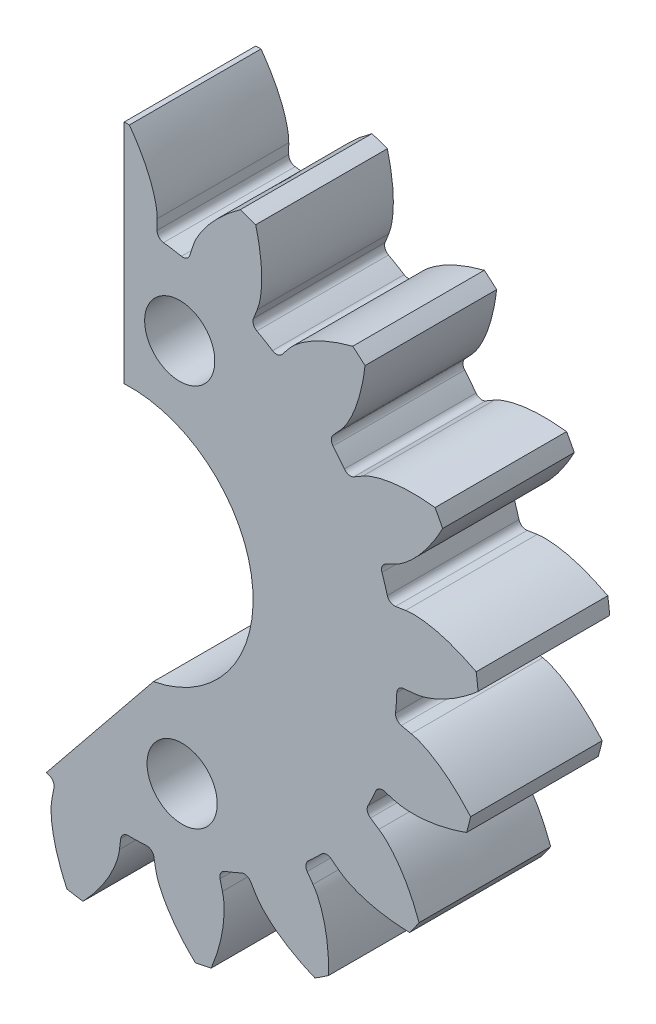
SolidWorks part; units mm, degrees
ref_plane "Front" through (0, 0, 0) normal (0, 0, 1) x (1, 0, 0)
ref_plane "Top" through (0, 0, 0) normal (0, 1, 0) x (1, 0, 0)
ref_plane "Right" through (0, 0, 0) normal (1, 0, 0) x (0, 0, -1)
sketch "Sketch1" plane through (0, 0, 0) normal (0, 0, 1) x (1, 0, 0)
  line L68 (2.1427, 9.4464) -> (2.0368, 9.1165)
  line L69 (0.916, 9.2963) -> (0.9185, 9.6427)
  line L70 (-1.4144, 9.5825) -> (-1.394, 9.2367)
  line L71 (-2.504, 8.9994) -> (-2.6268, 9.3234)
  line L72 (-4.7805, 8.4245) -> (-4.6366, 8.1093)
  line L73 (-5.5859, 7.4871) -> (-5.8174, 7.7449)
  line L74 (-7.501, 6.1287) -> (-7.2529, 5.8868)
  line L75 (-7.9134, 4.9637) -> (-8.2224, 5.1204)
  line L76 (-9.2084, 3.0052) -> (-8.8897, 2.8692)
  line L77 (-9.1721, 1.7699) -> (-9.5168, 1.8043)
  line L78 (-9.6722, -0.5242) -> (-9.3259, -0.5358)
  line L79 (-9.1921, -1.663) -> (-9.526, -1.7554)
  line L80 (-8.8296, -3.9828) -> (-8.5026, -3.8686)
  line L81 (-7.9706, -4.8713) -> (-8.2486, -5.078)
  line L82 (-6.7946, -6.9035) -> (-6.5309, -6.6788)
  line L83 (-5.6727, -7.4216) -> (-5.8572, -7.7148)
  line L84 (-3.842, -8.8918) -> (-3.6772, -8.587)
  line L85 (-2.6086, -8.9696) -> (-2.6747, -9.3097)
  line L86 (-0.3704, -9.6793) -> (-0.3269, -9.3356)
  line L87 (0.8078, -9.3063) -> (0.8689, -9.6473)
  line L88 (3.1511, -9.1595) -> (3.0675, -8.8232)
  line L89 (4.115, -8.3861) -> (4.2953, -8.6819)
  line L90 (6.2471, -7.4026) -> (6.0477, -7.1193)
  line L91 (6.8665, -6.3332) -> (7.1415, -6.544)
  line L92 (8.4994, -4.646) -> (8.2111, -4.4539)
  line L93 (8.6907, -3.4251) -> (9.0232, -3.5223)
  line L94 (9.6038, -1.2619) -> (9.2656, -1.1869)
  line L95 (9.3411, -0.0544) -> (9.6863, -0.0249)
  line L96 (9.4111, 2.2926) -> (9.0686, 2.2404)
  line L97 (8.73, 3.3237) -> (9.0412, 3.4759)
  line L98 (7.9475, 5.5374) -> (7.6469, 5.365)
  line L99 (6.9398, 6.2529) -> (7.1751, 6.5072)
  line L100 (5.4104, 8.0345) -> (5.1925, 7.7651)
  line L101 (4.2123, 8.3376) -> (4.3399, 8.6597)
  circle A0 centre (0, 0) radius 1.5
  arc A136 (4.2867, 11.1494) -> (3.764, 11.3366) centre (0, 0) ccw
  arc A137 (1.7491, 8.9466) -> (2.0368, 9.1165) centre (1.7973, 9.1934) ccw
  arc A138 (1.7491, 8.9466) -> (1.1361, 9.0449) centre (0, 0) ccw
  arc A139 (0.916, 9.2963) -> (1.1361, 9.0449) centre (1.1675, 9.2944) ccw
  arc A140 (-0.0304, 11.945) -> (-0.5854, 11.9307) centre (0, 0) ccw
  arc A141 (-1.6009, 8.9743) -> (-1.394, 9.2367) centre (-1.6451, 9.2219) ccw
  arc A142 (-1.6009, 8.9743) -> (-2.208, 8.8445) centre (0, 0) ccw
  arc A143 (-2.504, 8.9994) -> (-2.208, 8.8445) centre (-2.2689, 9.0885) ccw
  arc A144 (-4.3434, 11.1274) -> (-4.8558, 10.9136) centre (0, 0) ccw
  arc A145 (-4.7347, 7.79) -> (-4.6366, 8.1093) centre (-4.8653, 8.0049) ccw
  arc A146 (-4.7347, 7.79) -> (-5.2539, 7.4497) centre (0, 0) ccw
  arc A147 (-5.5859, 7.4871) -> (-5.2539, 7.4497) centre (-5.3988, 7.6552) ccw
  arc A148 (-8.0698, 8.807) -> (-8.4703, 8.4225) centre (0, 0) ccw
  arc A149 (-7.229, 5.5536) -> (-7.2529, 5.8868) centre (-7.4285, 5.7068) ccw
  arc A150 (-7.229, 5.5536) -> (-7.5902, 5.0487) centre (0, 0) ccw
  arc A151 (-7.9134, 4.9637) -> (-7.5902, 5.0487) centre (-7.7996, 5.188) ccw
  arc A152 (-10.7063, 5.2971) -> (-10.9409, 4.7939) centre (0, 0) ccw
  arc A153 (-8.7471, 2.5671) -> (-8.8897, 2.8692) centre (-8.9884, 2.6379) ccw
  arc A154 (-8.7471, 2.5671) -> (-8.9015, 1.9659) centre (0, 0) ccw
  arc A155 (-9.1721, 1.7699) -> (-8.9015, 1.9659) centre (-9.147, 2.0201) ccw
  arc A156 (-11.8969, 1.0719) -> (-11.9338, 0.5179) centre (0, 0) ccw
  arc A157 (-9.0837, -0.766) -> (-9.3259, -0.5358) centre (-9.3343, -0.7872) ccw
  arc A158 (-9.0837, -0.766) -> (-9.0105, -1.3825) centre (0, 0) ccw
  arc A159 (-9.1921, -1.663) -> (-9.0105, -1.3825) centre (-9.2591, -1.4206) ccw
  arc A160 (-11.4807, -3.2982) -> (-11.3151, -3.8281) centre (0, 0) ccw
  arc A161 (-8.1936, -3.9957) -> (-8.5026, -3.8686) centre (-8.4196, -4.106) ccw
  arc A162 (-8.1936, -3.9957) -> (-7.9027, -4.5441) centre (0, 0) ccw
  arc A163 (-7.9706, -4.8713) -> (-7.9027, -4.5441) centre (-8.1207, -4.6695) ccw
  arc A164 (-9.514, -7.2228) -> (-9.1681, -7.6571) centre (0, 0) ccw
  arc A165 (-6.1969, -6.6858) -> (-6.5309, -6.6788) centre (-6.3678, -6.8702) ccw
  arc A166 (-6.1969, -6.6858) -> (-5.7275, -7.092) centre (0, 0) ccw
  arc A167 (-5.6727, -7.4216) -> (-5.7275, -7.092) centre (-5.8855, -7.2877) ccw
  arc A168 (-6.2624, -10.1719) -> (-5.783, -10.4519) centre (0, 0) ccw
  arc A169 (-3.3632, -8.4729) -> (-3.6772, -8.587) centre (-3.456, -8.7066) ccw
  arc A170 (-3.3632, -8.4729) -> (-2.7788, -8.6821) centre (0, 0) ccw
  arc A171 (-2.6086, -8.9696) -> (-2.7788, -8.6821) centre (-2.8554, -8.9216) ccw
  arc A172 (-2.165, -11.7472) -> (-1.6168, -11.8352) centre (0, 0) ccw
  arc A173 (-0.0754, -9.1157) -> (-0.3269, -9.3356) centre (-0.0774, -9.3671) ccw
  arc A174 (-0.0754, -9.1157) -> (0.5452, -9.0997) centre (0, 0) ccw
  arc A175 (0.8078, -9.3063) -> (0.5452, -9.0997) centre (0.5602, -9.3507) ccw
  arc A176 (2.2248, -11.7361) -> (2.7677, -11.62) centre (0, 0) ccw
  arc A177 (3.2227, -8.5273) -> (3.0675, -8.8232) centre (3.3116, -8.7626) ccw
  arc A178 (3.2227, -8.5273) -> (3.7956, -8.2882) centre (0, 0) ccw
  arc A179 (4.115, -8.3861) -> (3.7956, -8.2882) centre (3.9003, -8.5169) ccw
  arc A180 (6.3141, -10.1399) -> (6.7785, -9.8355) centre (0, 0) ccw
  arc A181 (6.0855, -6.7873) -> (6.0477, -7.1193) centre (6.2534, -6.9746) ccw
  arc A182 (6.0855, -6.7873) -> (6.5333, -6.3574) centre (0, 0) ccw
  arc A183 (6.8665, -6.3332) -> (6.5333, -6.3574) centre (6.7135, -6.5328) ccw
  arc A184 (9.5507, -7.1742) -> (9.8737, -6.7227) centre (0, 0) ccw
  arc A185 (8.1264, -4.1307) -> (8.2111, -4.4539) centre (8.3506, -4.2446) ccw
  arc A186 (8.1264, -4.1307) -> (8.3887, -3.568) centre (0, 0) ccw
  arc A187 (8.6907, -3.4251) -> (8.3887, -3.568) centre (8.6201, -3.6665) ccw
  arc A188 (11.4974, -3.2397) -> (11.6355, -2.7019) centre (0, 0) ccw
  arc A189 (9.0698, -0.9161) -> (9.2656, -1.1869) centre (9.32, -0.9414) ccw
  arc A190 (9.0698, -0.9161) -> (9.1112, -0.2967) centre (0, 0) ccw
  arc A191 (9.3411, -0.0544) -> (9.1112, -0.2967) centre (9.3625, -0.3049) ccw
  arc A192 (11.8913, 1.1324) -> (11.8258, 1.6838) centre (0, 0) ccw
  arc A193 (8.7883, 2.4221) -> (9.0686, 2.2404) centre (9.0307, 2.489) ccw
  arc A194 (8.7883, 2.4221) -> (8.6031, 3.0146) centre (0, 0) ccw
  arc A195 (8.73, 3.3237) -> (8.6031, 3.0146) centre (8.8404, 3.0978) ccw
  arc A196 (10.6792, 5.3516) -> (10.419, 5.842) centre (0, 0) ccw
  arc A197 (7.3199, 5.4333) -> (7.6469, 5.365) centre (7.5218, 5.5832) ccw
  arc A198 (7.3199, 5.4333) -> (6.9331, 5.9189) centre (0, 0) ccw
  arc A199 (6.9398, 6.2529) -> (6.9331, 5.9189) centre (7.1244, 6.0821) ccw
  arc A200 (8.0248, 8.848) -> (7.605, 9.2113) centre (0, 0) ccw
  arc A201 (4.8629, 7.7106) -> (5.1925, 7.7651) centre (4.997, 7.9233) ccw
  arc A202 (4.8629, 7.7106) -> (4.3268, 8.0237) centre (0, 0) ccw
  arc A203 (4.2123, 8.3376) -> (4.3268, 8.0237) centre (4.4462, 8.245) ccw
  spline S68 degree 3 poles (3.764, 11.3366) (3.2587, 10.9714) (2.6231, 10.3935) (2.2067, 9.6531) (2.1427, 9.4464) knots -0.008485 -0.008485 -0.008485 -0.008485 0.741457 1 1 1 1
  spline S69 degree 3 poles (0.9185, 9.6427) (0.9201, 9.8535) (0.7567, 10.6863) (0.3366, 11.435) (-0.0304, 11.945) knots 0 0 0 0 0.250058 1 1 1 1
  spline S70 degree 3 poles (-0.5854, 11.9307) (-0.9247, 11.4077) (-1.3085, 10.6392) (-1.4294, 9.7984) (-1.4144, 9.5825) knots -0.008485 -0.008485 -0.008485 -0.008485 0.741457 1 1 1 1
  spline S71 degree 3 poles (-2.6268, 9.3234) (-2.7015, 9.5204) (-3.1547, 10.238) (-3.8169, 10.7844) (-4.3434, 11.1274) knots 0 0 0 0 0.250058 1 1 1 1
  spline S72 degree 3 poles (-4.8558, 10.9136) (-4.9832, 10.3033) (-5.0635, 9.4481) (-4.8725, 8.6204) (-4.7805, 8.4245) knots -0.008485 -0.008485 -0.008485 -0.008485 0.741457 1 1 1 1
  spline S73 degree 3 poles (-5.8174, 7.7449) (-5.9583, 7.9016) (-6.64, 8.4071) (-7.455, 8.6773) (-8.0698, 8.807) knots 0 0 0 0 0.250058 1 1 1 1
  spline S74 degree 3 poles (-8.4703, 8.4225) (-8.3687, 7.8074) (-8.1346, 6.9809) (-7.6575, 6.2781) (-7.501, 6.1287) knots -0.008485 -0.008485 -0.008485 -0.008485 0.741457 1 1 1 1
  spline S75 degree 3 poles (-8.2224, 5.1204) (-8.4103, 5.2157) (-9.2286, 5.4407) (-10.0862, 5.3983) (-10.7063, 5.2971) knots 0 0 0 0 0.250058 1 1 1 1
  spline S76 degree 3 poles (-10.9409, 4.7939) (-10.624, 4.2571) (-10.1071, 3.5709) (-9.4083, 3.088) (-9.2084, 3.0052) knots -0.008485 -0.008485 -0.008485 -0.008485 0.741457 1 1 1 1
  spline S77 degree 3 poles (-9.5168, 1.8043) (-9.7265, 1.8253) (-10.5708, 1.7395) (-11.3552, 1.3902) (-11.8969, 1.0719) knots 0 0 0 0 0.250058 1 1 1 1
  spline S78 degree 3 poles (-11.9338, 0.5179) (-11.4444, 0.1318) (-10.7145, -0.3213) (-9.8885, -0.5192) (-9.6722, -0.5242) knots -0.008485 -0.008485 -0.008485 -0.008485 0.741457 1 1 1 1
  spline S79 degree 3 poles (-9.526, -1.7554) (-9.7291, -1.8116) (-10.4854, -2.1966) (-11.0906, -2.8056) (-11.4807, -3.2982) knots 0 0 0 0 0.250058 1 1 1 1
  spline S80 degree 3 poles (-11.3151, -3.8281) (-10.7192, -4.0113) (-9.875, -4.1701) (-9.0332, -4.0563) (-8.8296, -3.9828) knots -0.008485 -0.008485 -0.008485 -0.008485 0.741457 1 1 1 1
  spline S81 degree 3 poles (-8.2486, -5.078) (-8.4177, -5.2038) (-8.9839, -5.836) (-9.3281, -6.6225) (-9.514, -7.2228) knots 0 0 0 0 0.250058 1 1 1 1
  spline S82 degree 3 poles (-9.1681, -7.6571) (-8.5463, -7.6126) (-7.7017, -7.4558) (-6.9579, -7.0456) (-6.7946, -6.9035) knots -0.008485 -0.008485 -0.008485 -0.008485 0.741457 1 1 1 1
  spline S83 degree 3 poles (-5.8572, -7.7148) (-5.9694, -7.8932) (-6.269, -8.6873) (-6.3059, -9.545) (-6.2624, -10.1719) knots 0 0 0 0 0.250058 1 1 1 1
  spline S84 degree 3 poles (-5.783, -10.4519) (-5.2192, -10.1859) (-4.4883, -9.7345) (-3.9429, -9.0833) (-3.842, -8.8918) knots -0.008485 -0.008485 -0.008485 -0.008485 0.741457 1 1 1 1
  spline S85 degree 3 poles (-2.6747, -9.3097) (-2.715, -9.5166) (-2.7074, -10.3653) (-2.432, -11.1784) (-2.165, -11.7472) knots 0 0 0 0 0.250058 1 1 1 1
  spline S86 degree 3 poles (-1.6168, -11.8352) (-1.1872, -11.3834) (-0.6687, -10.6985) (-0.3954, -9.8942) (-0.3704, -9.6793) knots -0.008485 -0.008485 -0.008485 -0.008485 0.741457 1 1 1 1
  spline S87 degree 3 poles (0.8689, -9.6473) (0.9062, -9.8547) (1.2197, -10.6434) (1.7703, -11.3021) (2.2248, -11.7361) knots 0 0 0 0 0.250058 1 1 1 1
  spline S88 degree 3 poles (2.7677, -11.62) (3.0051, -11.0436) (3.2412, -10.2176) (3.2055, -9.3689) (3.1511, -9.1595) knots -0.008485 -0.008485 -0.008485 -0.008485 0.741457 1 1 1 1
  spline S89 degree 3 poles (4.2953, -8.6819) (4.4049, -8.8619) (4.9822, -9.484) (5.7336, -9.8994) (6.3141, -10.1399) knots 0 0 0 0 0.250058 1 1 1 1
  spline S90 degree 3 poles (6.7785, -9.8355) (6.7916, -9.2122) (6.7134, -8.3568) (6.3735, -7.5783) (6.2471, -7.4026) knots -0.008485 -0.008485 -0.008485 -0.008485 0.741457 1 1 1 1
  spline S91 degree 3 poles (7.1415, -6.544) (7.3088, -6.6723) (8.0718, -7.0438) (8.9225, -7.1597) (9.5507, -7.1742) knots 0 0 0 0 0.250058 1 1 1 1
  spline S92 degree 3 poles (9.8737, -6.7227) (9.6608, -6.1367) (9.2788, -5.3673) (8.6807, -4.7642) (8.4994, -4.646) knots -0.008485 -0.008485 -0.008485 -0.008485 0.741457 1 1 1 1
  spline S93 degree 3 poles (9.0232, -3.5223) (9.2255, -3.5815) (10.0712, -3.6523) (10.9064, -3.4531) (11.4974, -3.2397) knots 0 0 0 0 0.250058 1 1 1 1
  spline S94 degree 3 poles (11.6355, -2.7019) (11.2253, -2.2324) (10.5911, -1.653) (9.8155, -1.3066) (9.6038, -1.2619) knots -0.008485 -0.008485 -0.008485 -0.008485 0.741457 1 1 1 1
  spline S95 degree 3 poles (9.6863, -0.0249) (9.8963, -0.007) (10.7105, 0.2325) (11.4173, 0.7199) (11.8913, 1.1324) knots 0 0 0 0 0.250058 1 1 1 1
  spline S96 degree 3 poles (11.8258, 1.6838) (11.2737, 1.9734) (10.4731, 2.2846) (9.6247, 2.3274) (9.4111, 2.2926) knots -0.008485 -0.008485 -0.008485 -0.008485 0.741457 1 1 1 1
  spline S97 degree 3 poles (9.0412, 3.4759) (9.2306, 3.5684) (9.9033, 4.0859) (10.3862, 4.7957) (10.6792, 5.3516) knots 0 0 0 0 0.250058 1 1 1 1
  spline S98 degree 3 poles (10.419, 5.842) (9.7996, 5.9126) (8.9406, 5.9136) (8.134, 5.6471) (7.9475, 5.5374) knots -0.008485 -0.008485 -0.008485 -0.008485 0.741457 1 1 1 1
  spline S99 degree 3 poles (7.1751, 6.5072) (7.3182, 6.6619) (7.7585, 7.3874) (7.9524, 8.2238) (8.0248, 8.848) knots 0 0 0 0 0.250058 1 1 1 1
  spline S100 degree 3 poles (7.605, 9.2113) (7.002, 9.0534) (6.2006, 8.744) (5.5448, 8.2041) (5.4104, 8.0345) knots -0.008485 -0.008485 -0.008485 -0.008485 0.741457 1 1 1 1
  spline S101 degree 3 poles (4.3399, 8.6597) (4.4174, 8.8557) (4.566, 9.6913) (4.4446, 10.5412) (4.2867, 11.1494) knots 0 0 0 0 0.250058 1 1 1 1
  dimension "D1" = 3
extrude "Boss-Extrude1" add sketch "Sketch1" along normal blind 4.5
sketch "Sketch3" plane through (0, 0, 4.5) normal (0, 0, 1) x (1, 0, 0)
  line L0 (0, 0) -> (-24.6444, 0)
sketch "Sketch4" plane through (0, 0, 0) normal (0, 0, -1) x (-1, 0, 0)
  line L0 (12.8632, 15.1898) -> (0.2099, 15.1898)
  line L1 (3.0728, -8.5825) -> (3.0728, -14.2917) construction
  line L2 (3.0728, -14.2917) -> (12.6632, -14.2917) construction
  line L4 (3.0728, -8.5825) -> (-0.6826, -3.9413) construction
  line L5 (12.6632, -14.2917) -> (12.6632, 14.9898) construction
  line L6 (12.6632, 14.9898) -> (0.4099, 14.9898) construction
  line L7 (0.2099, 15.1898) -> (0.2099, 4.1947)
  line L8 (2.8728, -8.6533) -> (-0.7915, -4.1248)
  line L9 (2.8728, -8.6533) -> (2.8728, -14.4917)
  line L10 (2.8728, -14.4917) -> (12.8632, -14.4917)
  line L11 (12.8632, -14.4917) -> (12.8632, 15.1898)
  line L22 (0.4099, 14.9898) -> (0.4099, 3.9789) construction
  arc A0 (0.2099, 4.1947) -> (-0.7915, -4.1248) centre (0, 0) ccw
  arc A3 (0.4099, 3.9789) -> (-0.6826, -3.9413) centre (0, 0) ccw construction
  dimension "D1" = 0.2
extrude "Cut-Extrude1" cut sketch "Sketch4" against normal through all
sketch "Sketch5" plane through (0, 0, 4.5) normal (0, 0, 1) x (1, 0, 0)
  line L1 (-0.2099, 11.9432) -> (-0.2099, 4.1947) construction
  circle A2 centre (1.6901, 6.4124) radius 1
  circle A3 centre (1.7728, -6.6584) radius 1
  dimension "D1" = 2
  dimension "D2" = 1.9
hole_wizard "CSK for M2 Countersunk Flat Head Screw1" positions "Sketch7" profile "Sketch8" countersink size "M2" standard "ISO"
sketch "Sketch7" plane through (0, 0, 0) normal (0, 0, 1) x (1, 0, 0)
  point P0 (1.6901, 6.4124)
  point P2 (1.7728, -6.6584)
  dimension "D1" = 1.6901
  dimension "D2" = 6.4124
  dimension "D3" = 1.7728
  dimension "D4" = 6.6584
sketch "Sketch8" plane through (1.6901, 6.4124, 0) normal (1, 0, 0) x (0, 1, 0)
  line L0 (0, 0) -> (0, 10.721)
  line L1 (0, 10.721) -> (1.2, 10)
  line L2 (1.2, 10) -> (1.2, 1)
  line L3 (1.2, 1) -> (2.2, 0)
  line L5 (2.2, 0) -> (0, 0)
  line L6 (-1.2, 1) -> (-2.2, 0) construction
  line L10 (0, 10.721) -> (-1.2, 10) construction
  line L11 (0, -6.35) -> (0, 107.95) construction
  dimension "Hole Dia." = 2.4
  dimension "Hole Depth" = 10
  dimension "Near C'Sink Dia." = 4.4
  dimension "Near C'Sink Angle" = 90
  dimension "Drill Angle" = 118
